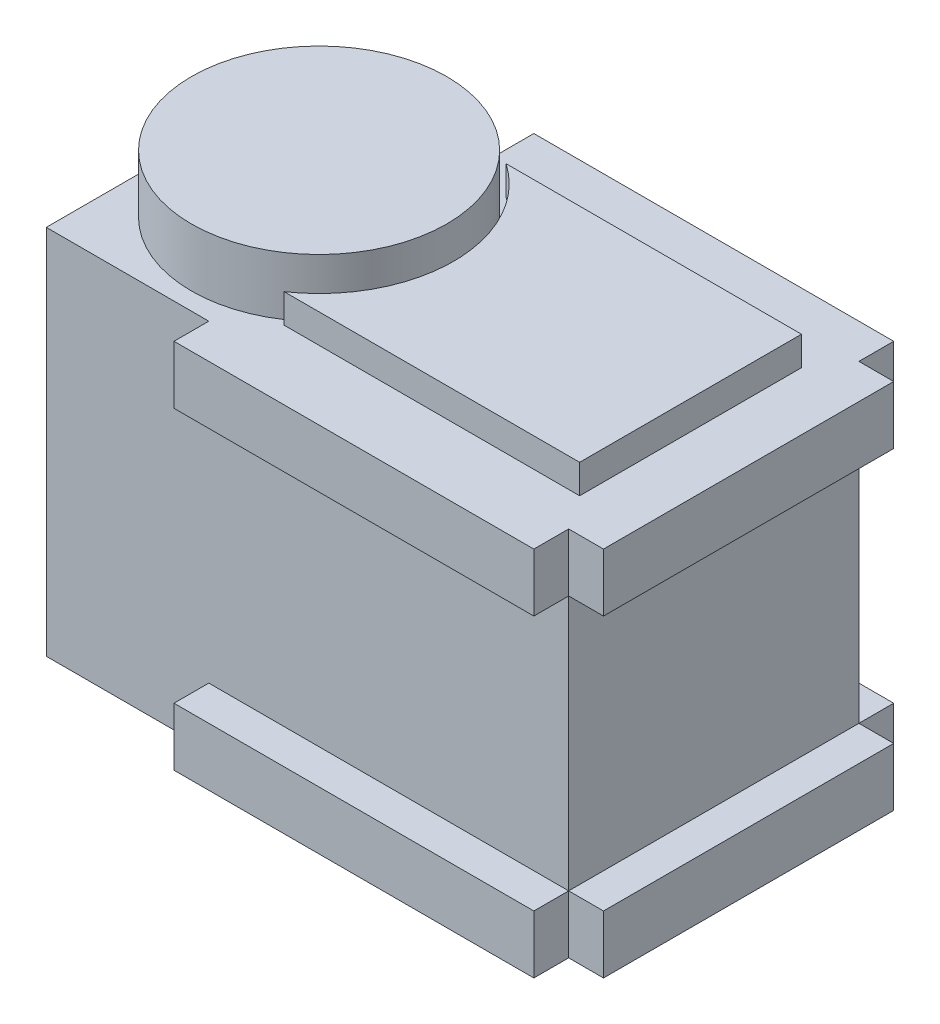
SolidWorks part; units mm, degrees
ref_plane "Front Plane" through (0, 0, 0) normal (0, 0, 1) x (1, 0, 0)
ref_plane "Top Plane" through (0, 0, 0) normal (0, 1, 0) x (1, 0, 0)
ref_plane "Right Plane" through (0, 0, 0) normal (1, 0, 0) x (0, 0, -1)
sketch "Sketch1" plane through (0, 0, 0) normal (0, 1, 0) x (1, 0, 0)
  line L1 (-22.5, -12.5) -> (22.5, -12.5)
  line L2 (-22.5, -12.5) -> (-22.5, 12.5)
  line L3 (-22.5, 12.5) -> (22.5, 12.5)
  line L4 (22.5, -12.5) -> (22.5, 12.5)
  line L5 (-22.5, -12.5) -> (22.5, 12.5) construction
  line L6 (-22.5, 12.5) -> (22.5, -12.5) construction
  point P0 (0, 0)
  dimension "D1" = 25
  dimension "D2" = 45
extrude "Boss-Extrude1" add sketch "Sketch1" along normal blind 32
sketch "Sketch2" plane through (0, 32, 0) normal (0, 1, 0) x (1, 0, 0)
  line L0 (-22.5, 12.5) -> (-22.5, -12.5) construction
  circle A0 centre (-11.5, 0) radius 11
  point P2 (-11.1685, 0)
  point P3 (-11.1064, 0)
  point P5 (-10.8705, 0)
  point P6 (-11.2479, 0)
  dimension "D1" = 22
  dimension "D2" = 11
extrude "Boss-Extrude2" add sketch "Sketch2" along normal blind 5
sketch "Sketch3" plane through (0, 32, 0) normal (0, 1, 0) x (1, 0, 0)
  line L1 (-4.9527, 9.5551) -> (20.5, 9.5551)
  line L3 (-4.9527, -9.5551) -> (20.5, -9.5551)
  line L4 (20.5, 9.5551) -> (20.5, -9.5551)
  arc A0 (-4.9527, -9.5551) -> (-4.9527, 9.5551) centre (-11.5, 0) ccw
  point P7 (-5.4165, -9.5551)
  dimension "D1" = 32
extrude "Boss-Extrude3" add sketch "Sketch3" along normal blind 2.5
sketch "Sketch4" plane through (0, 0, 12.5) normal (0, 0, 1) x (1, 0, 0)
  line L1 (22.5, 32) -> (-8.5, 32)
  line L2 (22.5, 32) -> (22.5, 27)
  line L3 (22.5, 27) -> (-8.5, 27)
  line L4 (-8.5, 32) -> (-8.5, 27)
  line L5 (22.5, 0) -> (-8.5, 0)
  line L6 (22.5, 0) -> (22.5, 5)
  line L7 (22.5, 5) -> (-8.5, 5)
  line L8 (-8.5, 0) -> (-8.5, 5)
  dimension "D1" = 31
  dimension "D2" = 5
  dimension "D3" = 5
extrude "Boss-Extrude4" add sketch "Sketch4" along normal blind 3
sketch "Sketch5" plane through (0, 0, -12.5) normal (0, 0, -1) x (-1, 0, 0)
  line L0 (8.5, 27) -> (-22.5, 27) construction
  line L1 (-22.5, 32) -> (8.5, 32)
  line L2 (-22.5, 32) -> (-22.5, 27)
  line L4 (8.5, 32) -> (8.5, 27)
  line L5 (8.5, 27) -> (-22.5, 27)
  line L7 (-22.5, 0) -> (8.5, 0)
  line L8 (-22.5, 0) -> (-22.5, 5)
  line L9 (-22.5, 5) -> (8.5, 5)
  line L10 (8.5, 0) -> (8.5, 5)
  dimension "D1" = 5
  dimension "D2" = 5
extrude "Boss-Extrude5" add sketch "Sketch5" along normal blind 3
sketch "Sketch6" plane through (22.5, 0, 0) normal (1, 0, 0) x (0, 0, -1)
  line L0 (-15.5, 0) -> (15.5, 0) construction
  line L1 (-12.5, 5) -> (12.5, 5)
  line L2 (-12.5, 5) -> (-12.5, 0)
  line L3 (-12.5, 0) -> (12.5, 0)
  line L4 (12.5, 5) -> (12.5, 0)
  line L5 (12.5, 27) -> (12.5, 5) construction
  line L6 (-15.5, 32) -> (15.5, 32) construction
  line L7 (-12.5, 27) -> (12.5, 27)
  line L8 (-12.5, 27) -> (-12.5, 32)
  line L9 (-12.5, 32) -> (12.5, 32)
  line L10 (12.5, 27) -> (12.5, 32)
extrude "Boss-Extrude6" add sketch "Sketch6" along normal blind 3
